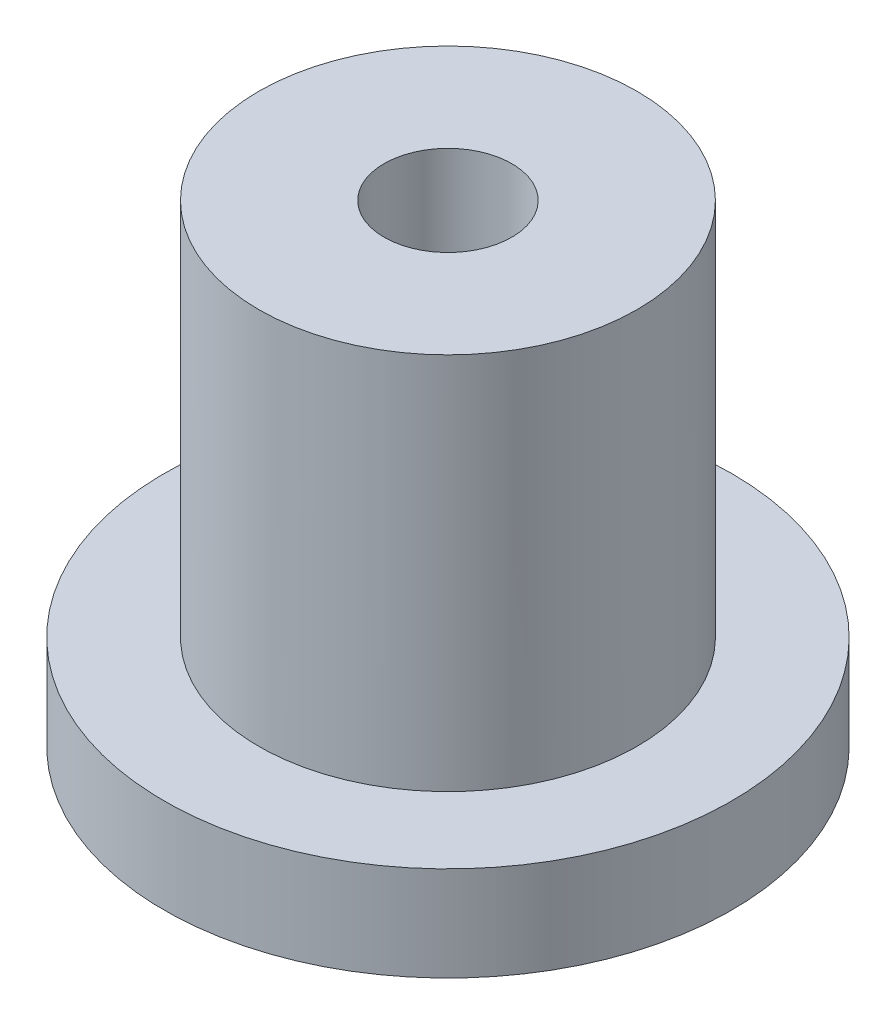
SolidWorks part; units mm, degrees
ref_plane "정면" through (0, 0, 0) normal (0, 0, 1) x (1, 0, 0)
ref_plane "윗면" through (0, 0, 0) normal (0, 1, 0) x (1, 0, 0)
ref_plane "우측면" through (0, 0, 0) normal (1, 0, 0) x (0, 0, -1)
sketch "스케치1" plane through (0, 0, 0) normal (0, 1, 0) x (1, 0, 0)
  circle A0 centre (0, 0) radius 4
  dimension "D1" = 8
extrude "보스-돌출1" add sketch "스케치1" along normal blind 8
sketch "스케치2" plane through (0, 8, 0) normal (0, 1, 0) x (1, 0, 0)
  circle A0 centre (0, 0) radius 1.35
  dimension "D1" = 2.7
sketch "스케치3" plane through (0, 0, 0) normal (0, -1, 0) x (1, 0, 0)
  circle A0 centre (0, 0) radius 6
  dimension "D1" = 12
extrude "보스-돌출2" add sketch "스케치3" along normal blind 2 contours A0
extrude "컷-돌출1" cut sketch "스케치2" against normal blind 12 contours A0
